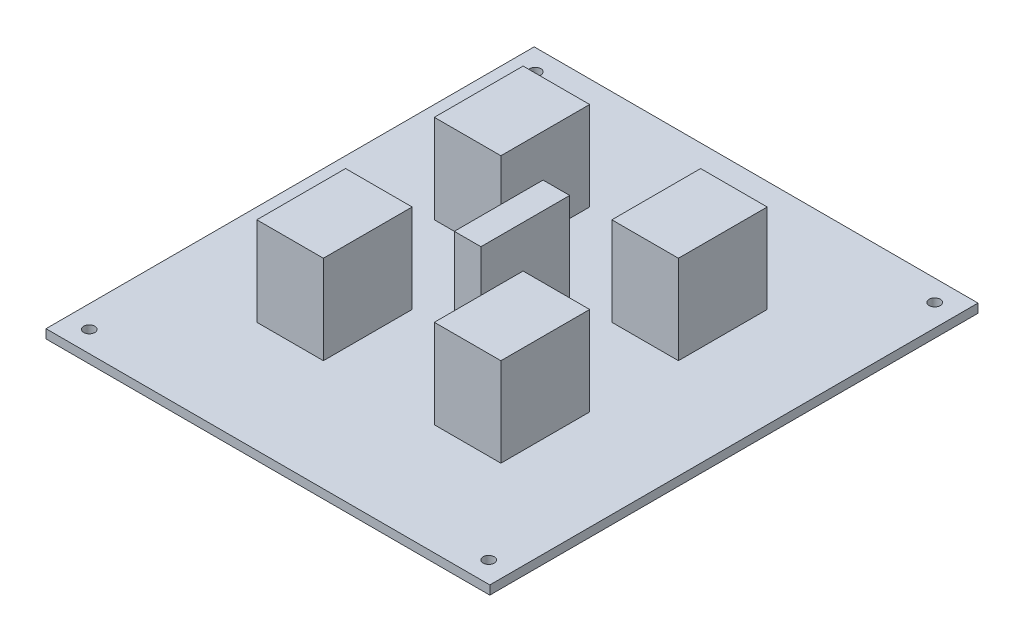
SolidWorks part; units mm, degrees
ref_plane "Front Plane" through (0, 0, 0) normal (0, 0, 1) x (1, 0, 0)
ref_plane "Top Plane" through (0, 0, 0) normal (0, 1, 0) x (1, 0, 0)
ref_plane "Right Plane" through (0, 0, 0) normal (1, 0, 0) x (0, 0, -1)
sketch "Sketch2" plane through (0, 0, 0) normal (0, 1, 0) x (1, 0, 0)
  line L0 (-45, 50.25) -> (45, 50.25) construction
  line L1 (-50, -55) -> (50, -55)
  line L2 (-50, -55) -> (-50, 55)
  line L3 (-50, 55) -> (50, 55)
  line L4 (50, -55) -> (50, 55)
  line L5 (-50, -55) -> (50, 55) construction
  line L6 (-50, 55) -> (50, -55) construction
  line L7 (-50, 0) -> (50, 0) construction
  line L8 (-45, -50.25) -> (45, -50.25) construction
  circle A0 centre (-45, 50.25) radius 1.25
  circle A1 centre (45, 50.25) radius 1.25
  circle A2 centre (45, -50.25) radius 1.25
  circle A3 centre (-45, -50.25) radius 1.25
  point P0 (0, 0)
  point P10 (0, 55)
  point P11 (0, 50.25)
  dimension "D3" = 2.5
  dimension "D1" = 110
  dimension "D2" = 100
  dimension "D4" = 90
  dimension "D5" = 4.75
extrude "Boss-Extrude1" add sketch "Sketch2" along normal blind 2
sketch "Sketch3" plane through (0, 2, 0) normal (0, 1, 0) x (1, 0, 0)
  line L0 (0, 55) -> (0, -55) construction
  line L5 (-27.5, 10) -> (-12.5, 30) construction
  line L6 (-27.5, 30) -> (-12.5, 10) construction
  line L7 (50, 55) -> (-50, 55) construction
  line L8 (-50, -55) -> (50, -55) construction
  line L9 (-27.5, -30) -> (-12.5, -30)
  line L14 (-27.5, -30) -> (-27.5, -10)
  line L15 (-27.5, -10) -> (-12.5, -10)
  line L16 (-12.5, -30) -> (-12.5, -10)
  line L17 (-27.5, -30) -> (-12.5, -10) construction
  line L18 (-27.5, -10) -> (-12.5, -30) construction
  line L23 (3, 10) -> (-3, 10)
  line L24 (-3, 10) -> (-3, -10)
  line L25 (-3, -10) -> (3, -10)
  line L26 (-50, 0) -> (50, 0) construction
  line L27 (-50, 55) -> (-50, -55) construction
  line L28 (50, -55) -> (50, 55) construction
  line L29 (-12.5, 30) -> (-12.5, 10)
  line L30 (-27.5, 10) -> (-12.5, 10)
  line L31 (-27.5, 30) -> (-27.5, 10)
  line L32 (-27.5, 30) -> (-12.5, 30)
  line L33 (27.5, -10) -> (12.5, -30) construction
  line L34 (27.5, -30) -> (12.5, -10) construction
  line L35 (27.5, 30) -> (12.5, 10) construction
  line L36 (27.5, 10) -> (12.5, 30) construction
  line L37 (27.5, 30) -> (12.5, 30)
  line L38 (27.5, 30) -> (27.5, 10)
  line L39 (27.5, 10) -> (12.5, 10)
  line L40 (12.5, 30) -> (12.5, 10)
  line L41 (3, 10) -> (3, -10)
  line L42 (12.5, -30) -> (12.5, -10)
  line L43 (27.5, -10) -> (12.5, -10)
  line L44 (27.5, -30) -> (27.5, -10)
  line L45 (27.5, -30) -> (12.5, -30)
  point P4 (-20, 20)
  point P12 (-20, -20)
  point P17 (20, -20)
  point P35 (0, -10)
  point P36 (0, 10)
  point P37 (20, 20)
  dimension "D1" = 3
  dimension "D2" = 10
  dimension "D3" = 10
  dimension "D4" = 20
  dimension "D5" = 12.5
  dimension "D6" = 15
  dimension "D7" = 10
extrude "Boss-Extrude2" add sketch "Sketch3" along normal blind 20
